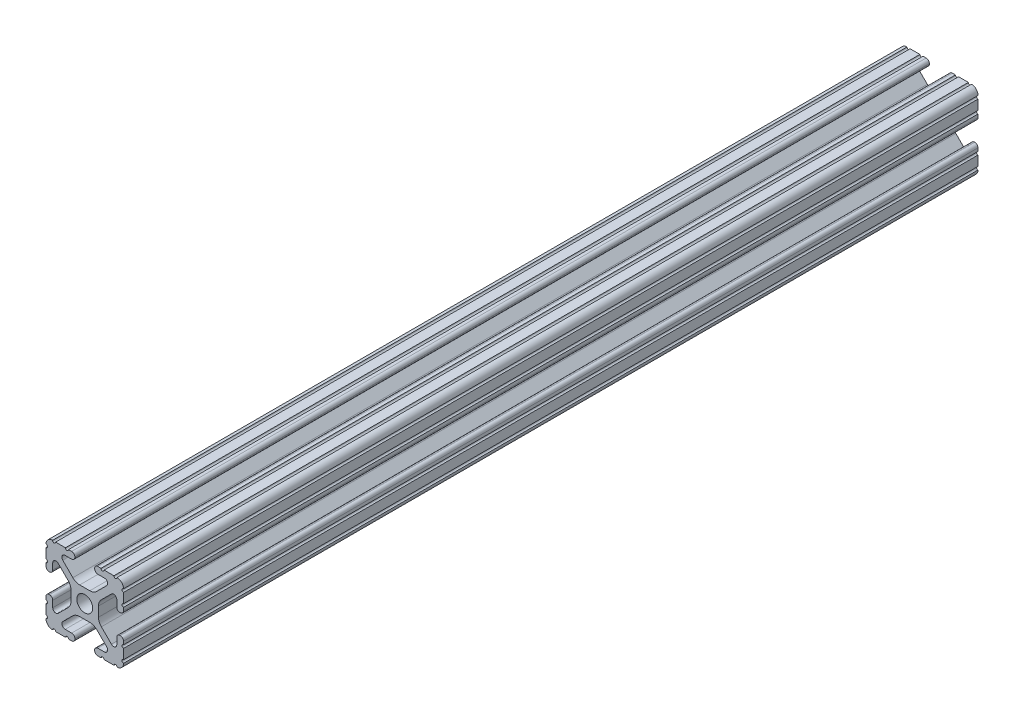
SolidWorks part; units mm, degrees
ref_plane "Front Plane" through (0, 0, 0) normal (0, 0, 1) x (1, 0, 0)
ref_plane "Top Plane" through (0, 0, 0) normal (0, 1, 0) x (1, 0, 0)
ref_plane "Right Plane" through (0, 0, 0) normal (1, 0, 0) x (0, 0, -1)
sketch "Sketch1" plane through (0, 0, 0) normal (0, 0, 1) x (1, 0, 0)
  line L88 (-7.1797, -8.6452) -> (-3.9523, -5.4237)
  line L89 (-1.7093, -4.4958) -> (1.7093, -4.4958)
  line L90 (3.9523, -5.4237) -> (7.1797, -8.6452)
  line L91 (6.4164, -10.4902) -> (4.2875, -10.4902)
  line L92 (3.2385, -11.5392) -> (3.2385, -11.651)
  line L93 (4.2875, -12.7) -> (5.3171, -12.7)
  line L94 (6.3331, -12.7) -> (9.5504, -12.7)
  line L95 (12.7, -9.5504) -> (12.7, -6.3331)
  line L96 (12.7, -5.3171) -> (12.7, -4.2875)
  line L97 (11.651, -3.2385) -> (11.5392, -3.2385)
  line L98 (10.4902, -4.2875) -> (10.4902, -6.4021)
  line L99 (8.7371, -7.1294) -> (5.441, -3.8408)
  line L100 (4.5085, -1.5932) -> (4.5085, 1.5932)
  line L101 (5.441, 3.8408) -> (8.7371, 7.1294)
  line L102 (10.4902, 6.4021) -> (10.4902, 4.2875)
  line L103 (11.5392, 3.2385) -> (11.651, 3.2385)
  line L104 (12.7, 4.2875) -> (12.7, 5.3171)
  line L105 (12.7, 6.3331) -> (12.7, 9.5504)
  line L106 (9.5504, 12.7) -> (6.3331, 12.7)
  line L107 (5.3171, 12.7) -> (4.2875, 12.7)
  line L108 (3.2385, 11.651) -> (3.2385, 11.5392)
  line L109 (4.2875, 10.4902) -> (6.4768, 10.4902)
  line L110 (7.207, 8.7244) -> (3.8983, 5.4232)
  line L111 (1.6558, 4.4958) -> (-1.6558, 4.4958)
  line L112 (-3.8983, 5.4232) -> (-7.207, 8.7244)
  line L113 (-6.4768, 10.4902) -> (-4.2875, 10.4902)
  line L114 (-3.2385, 11.5392) -> (-3.2385, 11.651)
  line L115 (-4.2875, 12.7) -> (-5.3171, 12.7)
  line L116 (-6.3331, 12.7) -> (-9.5504, 12.7)
  line L117 (-12.7, 9.5504) -> (-12.7, 6.3331)
  line L118 (-12.7, 5.3171) -> (-12.7, 4.2875)
  line L119 (-11.651, 3.2385) -> (-11.5392, 3.2385)
  line L120 (-10.4902, 4.2875) -> (-10.4902, 6.4021)
  line L121 (-8.7371, 7.1294) -> (-5.441, 3.8408)
  line L122 (-4.5085, 1.5932) -> (-4.5085, -1.5932)
  line L123 (-5.441, -3.8408) -> (-8.7371, -7.1294)
  line L124 (-10.4902, -6.4021) -> (-10.4902, -4.2875)
  line L125 (-11.5392, -3.2385) -> (-11.651, -3.2385)
  line L126 (-12.7, -4.2875) -> (-12.7, -5.3171)
  line L127 (-12.7, -6.3331) -> (-12.7, -9.5504)
  line L128 (-9.5504, -12.7) -> (-6.3331, -12.7)
  line L129 (-5.3171, -12.7) -> (-4.2875, -12.7)
  line L130 (-3.2385, -11.651) -> (-3.2385, -11.5392)
  line L131 (-4.2875, -10.4902) -> (-6.4164, -10.4902)
  circle A1 centre (0, 0) radius 2.6035
  arc A104 (-7.1797, -8.6452) -> (-6.4164, -10.4902) centre (-6.4164, -9.4098) ccw
  arc A105 (-1.7093, -4.4958) -> (-3.9523, -5.4237) centre (-1.7093, -7.6708) ccw
  arc A106 (3.9523, -5.4237) -> (1.7093, -4.4958) centre (1.7093, -7.6708) ccw
  arc A107 (6.4164, -10.4902) -> (7.1797, -8.6452) centre (6.4164, -9.4098) ccw
  arc A108 (4.2875, -10.4902) -> (3.2385, -11.5392) centre (4.2875, -11.5392) ccw
  arc A109 (3.2385, -11.651) -> (4.2875, -12.7) centre (4.2875, -11.651) ccw
  arc A110 (6.3331, -12.7) -> (5.3171, -12.7) centre (5.8251, -12.7) ccw
  arc A111 (10.5664, -12.6998) -> (9.5504, -12.7) centre (10.0584, -12.7) ccw
  arc A112 (10.5664, -12.6998) -> (12.6998, -10.5664) centre (10.5918, -10.5918) ccw
  arc A113 (12.7, -9.5504) -> (12.6998, -10.5664) centre (12.7, -10.0584) ccw
  arc A114 (12.7, -5.3171) -> (12.7, -6.3331) centre (12.7, -5.8251) ccw
  arc A115 (12.7, -4.2875) -> (11.651, -3.2385) centre (11.651, -4.2875) ccw
  arc A116 (11.5392, -3.2385) -> (10.4902, -4.2875) centre (11.5392, -4.2875) ccw
  arc A117 (8.7371, -7.1294) -> (10.4902, -6.4021) centre (9.4628, -6.4021) ccw
  arc A118 (4.5085, -1.5932) -> (5.441, -3.8408) centre (7.6835, -1.5932) ccw
  arc A119 (5.441, 3.8408) -> (4.5085, 1.5932) centre (7.6835, 1.5932) ccw
  arc A120 (10.4902, 6.4021) -> (8.7371, 7.1294) centre (9.4628, 6.4021) ccw
  arc A121 (10.4902, 4.2875) -> (11.5392, 3.2385) centre (11.5392, 4.2875) ccw
  arc A122 (11.651, 3.2385) -> (12.7, 4.2875) centre (11.651, 4.2875) ccw
  arc A123 (12.7, 6.3331) -> (12.7, 5.3171) centre (12.7, 5.8251) ccw
  arc A124 (12.6998, 10.5664) -> (12.7, 9.5504) centre (12.7, 10.0584) ccw
  arc A125 (12.6998, 10.5664) -> (10.5664, 12.6998) centre (10.5918, 10.5918) ccw
  arc A126 (9.5504, 12.7) -> (10.5664, 12.6998) centre (10.0584, 12.7) ccw
  arc A127 (5.3171, 12.7) -> (6.3331, 12.7) centre (5.8251, 12.7) ccw
  arc A128 (4.2875, 12.7) -> (3.2385, 11.651) centre (4.2875, 11.651) ccw
  arc A129 (3.2385, 11.5392) -> (4.2875, 10.4902) centre (4.2875, 11.5392) ccw
  arc A130 (7.207, 8.7244) -> (6.4768, 10.4902) centre (6.4768, 9.4563) ccw
  arc A131 (1.6558, 4.4958) -> (3.8983, 5.4232) centre (1.6558, 7.6708) ccw
  arc A132 (-3.8983, 5.4232) -> (-1.6558, 4.4958) centre (-1.6558, 7.6708) ccw
  arc A133 (-6.4768, 10.4902) -> (-7.207, 8.7244) centre (-6.4768, 9.4563) ccw
  arc A134 (-4.2875, 10.4902) -> (-3.2385, 11.5392) centre (-4.2875, 11.5392) ccw
  arc A135 (-3.2385, 11.651) -> (-4.2875, 12.7) centre (-4.2875, 11.651) ccw
  arc A136 (-6.3331, 12.7) -> (-5.3171, 12.7) centre (-5.8251, 12.7) ccw
  arc A137 (-10.5664, 12.6998) -> (-9.5504, 12.7) centre (-10.0584, 12.7) ccw
  arc A138 (-10.5664, 12.6998) -> (-12.6998, 10.5664) centre (-10.5918, 10.5918) ccw
  arc A139 (-12.7, 9.5504) -> (-12.6998, 10.5664) centre (-12.7, 10.0584) ccw
  arc A140 (-12.7, 5.3171) -> (-12.7, 6.3331) centre (-12.7, 5.8251) ccw
  arc A141 (-12.7, 4.2875) -> (-11.651, 3.2385) centre (-11.651, 4.2875) ccw
  arc A142 (-11.5392, 3.2385) -> (-10.4902, 4.2875) centre (-11.5392, 4.2875) ccw
  arc A143 (-8.7371, 7.1294) -> (-10.4902, 6.4021) centre (-9.4628, 6.4021) ccw
  arc A144 (-4.5085, 1.5932) -> (-5.441, 3.8408) centre (-7.6835, 1.5932) ccw
  arc A145 (-5.441, -3.8408) -> (-4.5085, -1.5932) centre (-7.6835, -1.5932) ccw
  arc A146 (-10.4902, -6.4021) -> (-8.7371, -7.1294) centre (-9.4628, -6.4021) ccw
  arc A147 (-10.4902, -4.2875) -> (-11.5392, -3.2385) centre (-11.5392, -4.2875) ccw
  arc A148 (-11.651, -3.2385) -> (-12.7, -4.2875) centre (-11.651, -4.2875) ccw
  arc A149 (-12.7, -6.3331) -> (-12.7, -5.3171) centre (-12.7, -5.8251) ccw
  arc A150 (-12.6998, -10.5664) -> (-12.7, -9.5504) centre (-12.7, -10.0584) ccw
  arc A151 (-12.6998, -10.5664) -> (-10.5664, -12.6998) centre (-10.5918, -10.5918) ccw
  arc A152 (-9.5504, -12.7) -> (-10.5664, -12.6998) centre (-10.0584, -12.7) ccw
  arc A153 (-5.3171, -12.7) -> (-6.3331, -12.7) centre (-5.8251, -12.7) ccw
  arc A154 (-4.2875, -12.7) -> (-3.2385, -11.651) centre (-4.2875, -11.651) ccw
  arc A155 (-3.2385, -11.5392) -> (-4.2875, -10.4902) centre (-4.2875, -11.5392) ccw
extrude "Boss-Extrude1" add sketch "Sketch1" along normal blind 280
